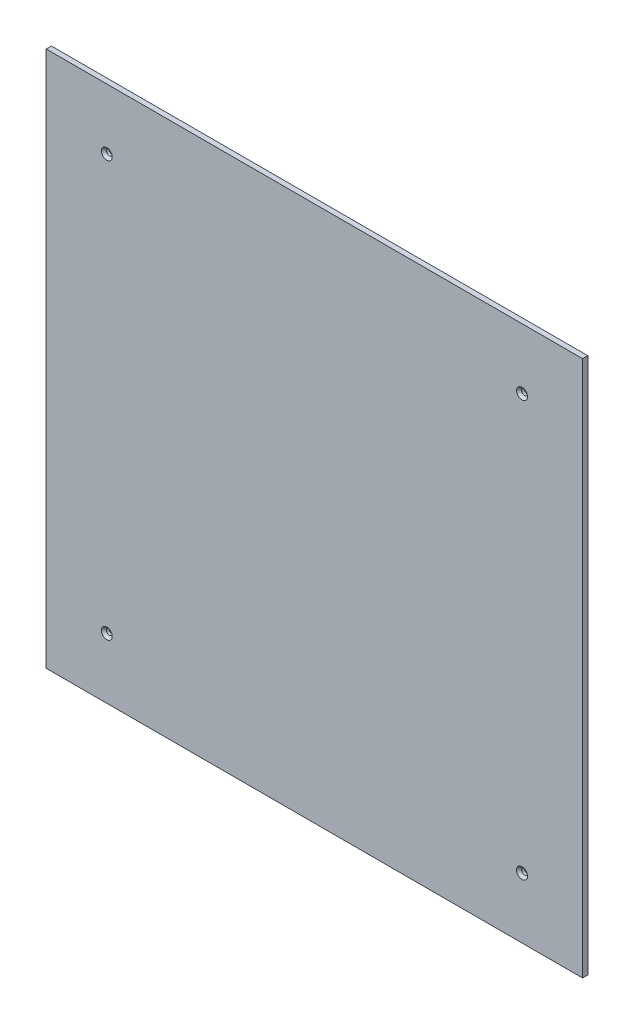
SolidWorks part; units mm, degrees
ref_plane "前视基准面" through (0, 0, 0) normal (0, 0, 1) x (1, 0, 0)
ref_plane "上视基准面" through (0, 0, 0) normal (0, 1, 0) x (1, 0, 0)
ref_plane "右视基准面" through (0, 0, 0) normal (1, 0, 0) x (0, 0, -1)
sketch "草图1" plane through (0, 0, 0) normal (0, 0, 1) x (1, 0, 0)
  line L1 (-143.2952, 104.9886) -> (166.7048, 104.9886)
  line L2 (-143.2952, 104.9886) -> (-143.2952, -205.0114)
  line L3 (-143.2952, -205.0114) -> (166.7048, -205.0114)
  line L4 (166.7048, 104.9886) -> (166.7048, -205.0114)
  dimension "D1" = 310
  dimension "D2" = 310
extrude "凸台-拉伸1" add sketch "草图1" against normal blind 3
sketch "草图2" plane through (0, 0, 0) normal (0, 0, 1) x (1, 0, 0)
  line L0 (-143.2952, -50.0114) -> (166.7048, -50.0114)
  line L1 (-143.2952, 104.9886) -> (-143.2952, -205.0114) construction
  line L2 (166.7048, -205.0114) -> (166.7048, 104.9886) construction
  line L3 (11.7048, 104.9886) -> (11.7048, -205.0114)
  line L4 (166.7048, 104.9886) -> (-143.2952, 104.9886) construction
  line L5 (-143.2952, -205.0114) -> (166.7048, -205.0114) construction
  line L6 (-202.8541, -170.0114) -> (212.1073, -170.0114)
  line L7 (212.1073, 69.9886) -> (-202.8541, 69.9886)
  line L8 (-108.2952, -226.9673) -> (-108.2952, 116.327)
  line L9 (131.7048, 116.327) -> (131.7048, -226.9673)
  dimension "D1" = 120
  dimension "D2" = 120
  dimension "D3" = 120
  dimension "D4" = 120
hole_wizard "M3 平头机械螺钉的锥形沉头孔1" positions "3D草图1" profile "草图3" countersink size "M3" standard "ANSI Metric" end condition through all
sketch3d "3D草图1"
  line L0 (212.1073, 69.9886, 0) -> (-202.8541, 69.9886, 0) construction
  line L1 (-108.2952, -226.9673, 0) -> (-108.2952, 116.327, 0) construction
  line L2 (131.7048, 116.327, 0) -> (131.7048, -226.9673, 0) construction
  line L3 (-202.8541, -170.0114, 0) -> (212.1073, -170.0114, 0) construction
  point P0 (-108.2952, 69.9886, 0)
  point P6 (131.7048, 69.9886, 0)
  point P10 (131.7048, -170.0114, 0)
  point P14 (-108.2952, -170.0114, 0)
sketch "草图3" plane through (-108.2952, 69.9886, 0) normal (1, 0, 0) x (0, -1, 0)
  line L0 (0, 0) -> (0, 3)
  line L1 (0, 3) -> (1.7, 3)
  line L2 (1.7, 3) -> (1.7, 1.45)
  line L3 (1.7, 1.45) -> (3.15, 0)
  line L5 (3.15, 0) -> (0, 0)
  line L6 (-1.7, 1.45) -> (-3.15, 0) construction
  line L11 (0, -6.35) -> (0, 107.95) construction
  dimension "通孔孔直径" = 3.4
  dimension "通孔孔深度" = 3
  dimension "近端锥形沉头孔直径" = 6.3
  dimension "近端锥形沉头孔角度" = 90
